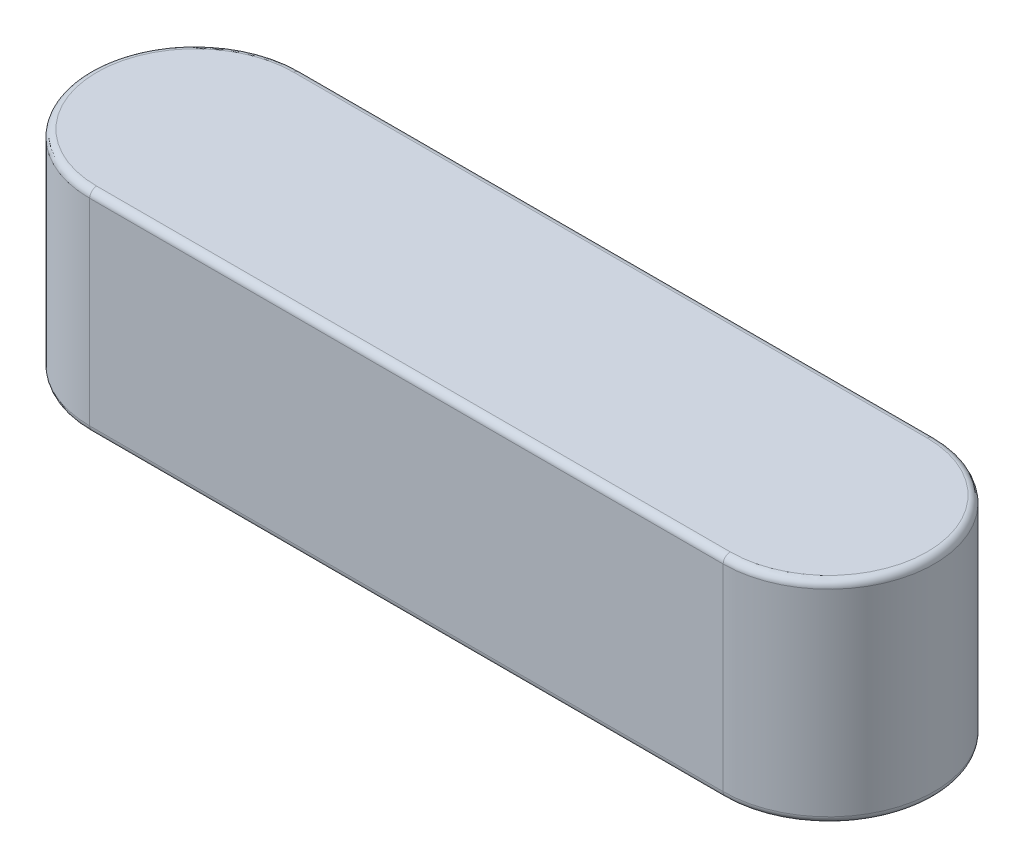
SolidWorks part; units mm, degrees
material "Acier C45E (1.1191)"
ref_plane "Plan de face" through (0, 0, 0) normal (0, 0, 1) x (1, 0, 0)
ref_plane "Plan de dessus" through (0, 0, 0) normal (0, 1, 0) x (1, 0, 0)
ref_plane "Plan de droite" through (0, 0, 0) normal (1, 0, 0) x (0, 0, -1)
sketch "Esquisse1" plane through (0, 0, 0) normal (0, 1, 0) x (1, 0, 0)
  line L0 (4.5, 0) -> (-4.5, 0) construction
  line L1 (4.5, -1.5) -> (-4.5, -1.5)
  line L2 (4.5, 1.5) -> (-4.5, 1.5)
  arc A0 (4.5, -1.5) -> (4.5, 1.5) centre (4.5, 0) ccw
  arc A1 (-4.5, 1.5) -> (-4.5, -1.5) centre (-4.5, 0) ccw
  point P2 (0, 0)
  point P8 (-6, 0)
  point P9 (6, 0)
  dimension "Largeur" = 3
  dimension "Longueur" = 12
extrude "Boss.-Extru.1" add sketch "Esquisse1" along normal blind 3
fillet "Congé1" radius 0.1 8 edges at (-6, 0, 0) (0, 0, -1.5) (6, 0, 0) (-6, 3, 0) (0, 3, -1.5) (6, 3, 0) (0, 0, 1.5) (0, 3, 1.5)
